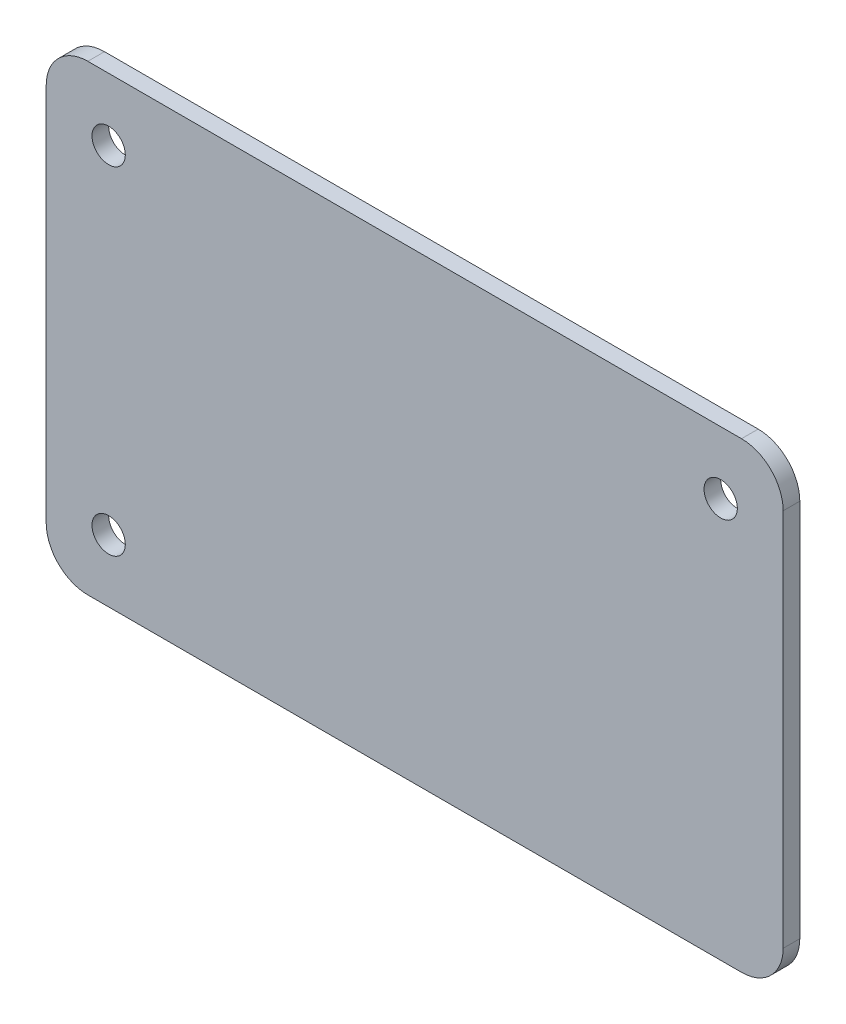
SolidWorks part; units mm, degrees
ref_plane "Plan de face" through (0, 0, 0) normal (0, 0, 1) x (1, 0, 0)
ref_plane "Plan de dessus" through (0, 0, 0) normal (0, 1, 0) x (1, 0, 0)
ref_plane "Plan de droite" through (0, 0, 0) normal (1, 0, 0) x (0, 0, -1)
sketch "Esquisse1" plane through (0, 0, 0) normal (0, 0, 1) x (1, 0, 0)
  line L0 (-73.5, 40.5) -> (-73.5, -40.5) construction
  line L1 (78.5, -55.5) -> (-78.5, -55.5)
  line L2 (88.5, -45.5) -> (88.5, 45.5)
  line L3 (78.5, 55.5) -> (-78.5, 55.5)
  line L4 (-88.5, -45.5) -> (-88.5, 45.5)
  line L5 (88.5, -55.5) -> (-88.5, 55.5) construction
  line L6 (88.5, 55.5) -> (-88.5, -55.5) construction
  line L7 (-73.5, -40.5) -> (73.5, -40.5) construction
  line L8 (73.5, -40.5) -> (73.5, 40.5) construction
  line L9 (73.5, 40.5) -> (-73.5, 40.5) construction
  circle A0 centre (-73.5, 40.5) radius 4
  circle A1 centre (73.5, 40.5) radius 4
  circle A3 centre (-73.5, -40.5) radius 4
  arc A4 (-78.5, -55.5) -> (-88.5, -45.5) centre (-78.5, -45.5) cw
  arc A5 (78.5, -55.5) -> (88.5, -45.5) centre (78.5, -45.5) ccw
  arc A6 (88.5, 45.5) -> (78.5, 55.5) centre (78.5, 45.5) ccw
  arc A7 (-78.5, 55.5) -> (-88.5, 45.5) centre (-78.5, 45.5) ccw
  point P0 (0, 0)
  dimension "D3" = 15
  dimension "D4" = 8
  dimension "D8" = 10
  dimension "D1" = 111
  dimension "D2" = 177
  dimension "D5" = 15
  dimension "D6" = 15
  dimension "D7" = 15
extrude "Boss.-Extru.1" add sketch "Esquisse1" along normal blind 4
